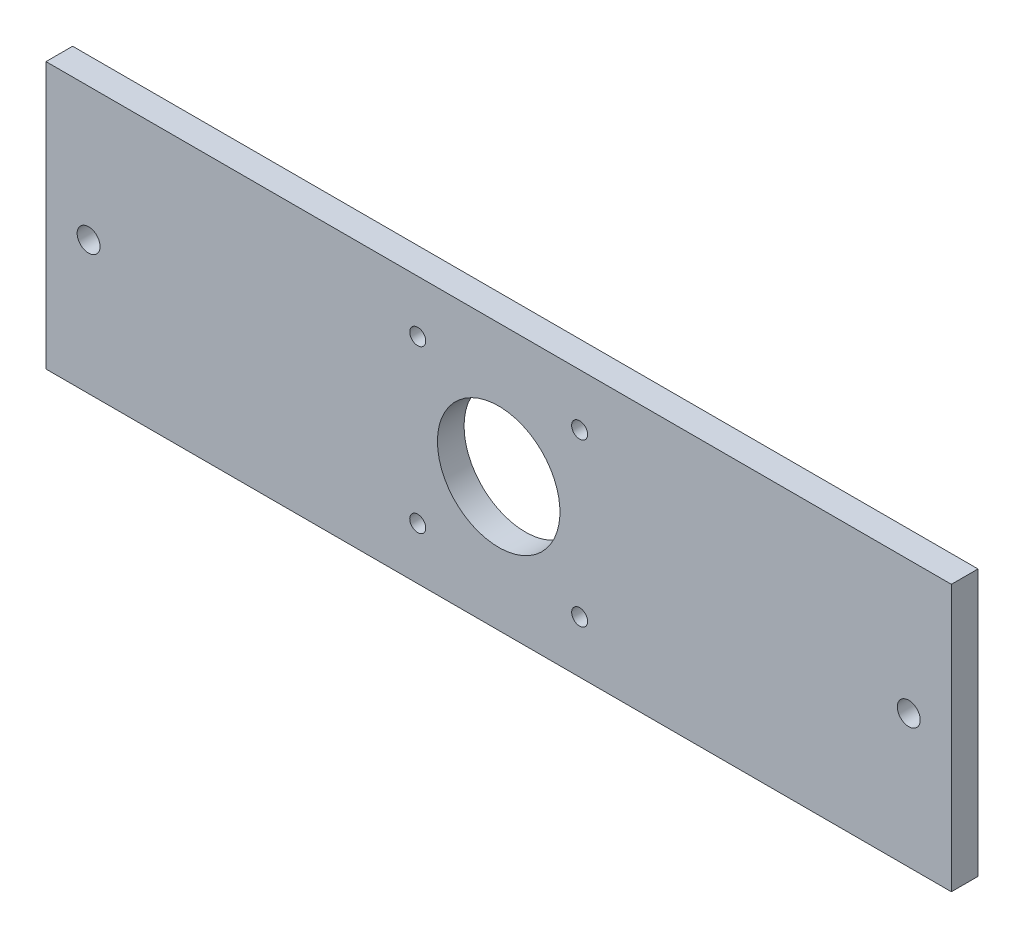
SolidWorks part; units mm, degrees
ref_plane "Plano frontal" through (0, 0, 0) normal (0, 0, 1) x (1, 0, 0)
ref_plane "Plano superior" through (0, 0, 0) normal (0, 1, 0) x (1, 0, 0)
ref_plane "Plano direito" through (0, 0, 0) normal (1, 0, 0) x (0, 0, -1)
sketch "Esboço1" plane through (0, 0, 0) normal (0, 0, 1) x (1, 0, 0)
  line L1 (0, 0) -> (50, 0)
  line L2 (0, 0) -> (0, 50)
  line L3 (0, 50) -> (50, 50)
  line L4 (50, 0) -> (50, 50)
  dimension "D1" = 50
  dimension "D2" = 50
extrude "Ressalto-extrusão1" add sketch "Esboço1" along normal blind 5
sketch "Esboço2" plane through (0, 0, 0) normal (0, 0, 1) x (1, 0, 0)
  line L1 (50, 0) -> (50, 50) construction
  circle A0 centre (25, 25) radius 11.5
  dimension "D1" = 23
extrude "Corte-extrusão1" cut sketch "Esboço2" along normal blind 8 and the other way blind 14
sketch "Esboço3" plane through (0, 0, 0) normal (0, 0, 1) x (1, 0, 0)
  line L1 (0, 50) -> (-60, 50)
  line L2 (0, 50) -> (0, 0)
  line L3 (0, 0) -> (-60, 0)
  line L4 (-60, 50) -> (-60, 0)
  line L5 (50, 50) -> (110, 50)
  line L6 (50, 50) -> (50, 0)
  line L7 (50, 0) -> (110, 0)
  line L8 (110, 50) -> (110, 0)
  dimension "D1" = 60
  dimension "D2" = 60
extrude "Ressalto-extrusão2" add sketch "Esboço3" along normal blind 5
sketch "Esboço4" plane through (0, 0, 0) normal (0, 0, 1) x (1, 0, 0)
  line L0 (-60, 25) -> (110, 25) construction
  line L1 (-60, 50) -> (-60, 0) construction
  line L2 (110, 0) -> (110, 50) construction
  line L3 (110, 25) -> (25, 0) construction
  line L4 (-60, 0) -> (110, 0) construction
  line L5 (25, 0) -> (25, 50) construction
  line L6 (110, 50) -> (-60, 50) construction
  line L7 (-60, 40.2) -> (110, 40.2) construction
  circle A0 centre (-52, 25) radius 2.15
  circle A1 centre (102, 25) radius 2.15
  circle A2 centre (9.8, 40.2) radius 1.5
  circle A3 centre (40.2, 40.2) radius 1.5
  circle A4 centre (40.2, 9.8) radius 1.5
  circle A5 centre (9.8, 9.8) radius 1.5
  point P29 (25, 25)
  dimension "D4" = 3
  dimension "D7" = 4.3
  dimension "D8" = 4.3
  dimension "D1" = 8
  dimension "D2" = 8
  dimension "D3" = 15.2
  dimension "D5" = 15.2
  dimension "D6" = 4
extrude "Corte-extrusão2" cut sketch "Esboço4" against normal blind 12 and the other way blind 19
